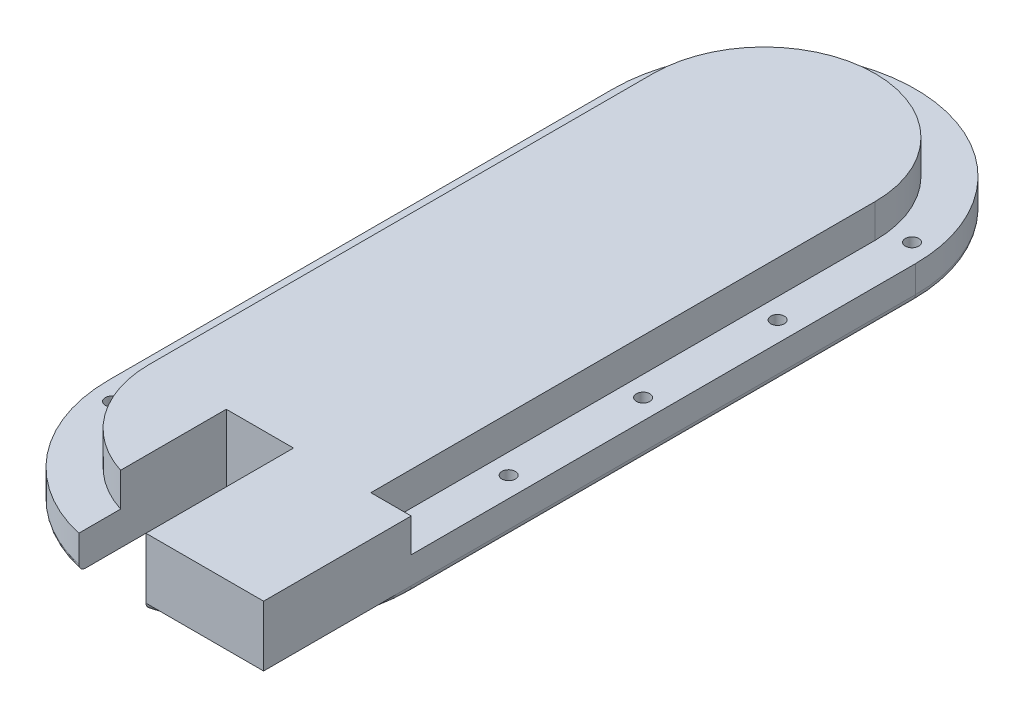
SolidWorks part; units mm, degrees
ref_plane "Front Plane" through (0, 0, 0) normal (0, 0, 1) x (1, 0, 0)
ref_plane "Top Plane" through (0, 0, 0) normal (0, 1, 0) x (1, 0, 0)
ref_plane "Right Plane" through (0, 0, 0) normal (1, 0, 0) x (0, 0, -1)
sketch "Sketch1" plane through (0, 0, 0) normal (0, 1, 0) x (1, 0, 0)
  line L0 (0, 0) -> (0, 150)
  line L1 (-90, 0) -> (-90, 150)
  arc A0 (-90, 150) -> (0, 150) centre (-45, 150) cw
  arc A1 (-90, 0) -> (0, 0) centre (-45, 0) ccw
  dimension "D1" = 90
  dimension "D2" = 150
  dimension "D3" = 150
extrude "Boss-Extrude1" add sketch "Sketch1" against normal blind 20
fillet "Fillet1" radius 2 8 edges at (0, -20, -75) (0, 0, -75) (-90, -20, -75) (-90, 0, -75) (-45, -20, -195) (-45, 0, -195) (-45, -20, 45) (-45, 0, 45)
sketch "Sketch4" plane through (0, -20, 0) normal (0, -1, 0) x (1, 0, 0)
  line L0 (-2, -150) -> (-89, -150) construction
  line L1 (-88, -150) -> (-90, -150) construction
  circle A0 centre (-45.5, -150) radius 11
  dimension "D1" = 22
extrude "Cut-Extrude2" cut sketch "Sketch4" against normal blind 6.35
sketch "Sketch5" plane through (0, 0, 0) normal (0, 1, 0) x (1, 0, 0)
  line L0 (-45, 0) -> (-45, 150) construction
  line L1 (-78, 0) -> (-78, 150)
  line L2 (-12, 0) -> (-12, 150)
  line L3 (-88, 150) -> (-88, 0) construction
  line L4 (-2, 0) -> (-2, 150) construction
  arc A0 (-78, 0) -> (-12, 0) centre (-45, 0) ccw
  arc A1 (-12, 150) -> (-78, 150) centre (-45, 150) ccw
  arc A2 (-2, 150) -> (-88, 150) centre (-45, 150) ccw construction
  arc A3 (-88, 0) -> (-2, 0) centre (-45, 0) ccw construction
  point P2 (-45, 75)
  point P21 (-45, -33)
  point P22 (-45, 183)
  dimension "D3" = 10
  dimension "D4" = 10
  dimension "D1" = 10
  dimension "D2" = 10
extrude "Cut-Extrude3" cut sketch "Sketch5" against normal blind 10 flip side to cut
sketch "Sketch7" plane through (0, -10, 0) normal (0, 1, 0) x (1, 0, 0)
  line L0 (-6, 0) -> (-6, 150) construction
  line L1 (-90, 0) -> (-90, 150) construction
  line L2 (0, 150) -> (0, 0) construction
  line L3 (-45, 195) -> (-45, -45) construction
  line L4 (-84, 0) -> (-84, 150) construction
  line L9 (-12, 0) -> (-12, 150) construction
  line L10 (-78, 150) -> (-78, 0) construction
  line L11 (-12, 75) -> (0, 75) construction
  line L12 (-77.984, 75) -> (-90, 75) construction
  arc A0 (0, 150) -> (-90, 150) centre (-45, 150) ccw construction
  arc A1 (-90, 0) -> (0, 0) centre (-45, 0) ccw construction
  circle A2 centre (-6, 75) radius 2
  circle A3 centre (-6, 115) radius 2
  circle A4 centre (-6, 155) radius 2
  circle A5 centre (-6, 35) radius 2
  circle A6 centre (-6, -5) radius 2
  circle A7 centre (-84, -5) radius 2
  circle A8 centre (-84, 35) radius 2
  circle A9 centre (-84, 75) radius 2
  circle A10 centre (-84, 115) radius 2
  circle A11 centre (-84, 155) radius 2
  point P18 (-6, 75)
  point P24 (-77.984, 75)
  point P25 (-12, 75)
  point P26 (-90, 75)
  point P27 (0, 75)
  point P28 (-78, 75)
  dimension "D1" = 4
  dimension "D2" = 3
extrude "Cut-Extrude4" cut sketch "Sketch7" against normal through all
ref_plane "Plane1" through (0, 0, 0) normal (0, 1, 0) x (1, 0, 0)
sketch "Sketch9" plane through (0, 0, 0) normal (0, 1, 0) x (1, 0, 0)
  line L0 (-12, 0) -> (-78, 0) construction
  line L1 (-55, 0) -> (-35, 0)
  line L2 (-35, 0) -> (-35, -50.9697)
  line L3 (-35, -50.9697) -> (-55, -50.9697)
  line L4 (-55, -50.9697) -> (-55, 0)
  point P7 (-45, 0)
  dimension "D1" = 20
extrude "Cut-Extrude6" cut sketch "Sketch9" against normal through all
ref_plane "Plane9" through (0, 0, 0) normal (0, 0, 1) x (1, 0, 0)
sketch "Sketch10" plane through (0, 0, 0) normal (0, 0, 1) x (1, 0, 0)
  line L0 (-35, 0) -> (0, 0)
  line L1 (-35, 0) -> (-35, -18)
  line L2 (-35, -18) -> (0, -18)
  line L4 (0, -18) -> (0, 0)
  dimension "D1" = 35
extrude "Boss-Extrude2" add sketch "Sketch10" along normal blind 43.9
